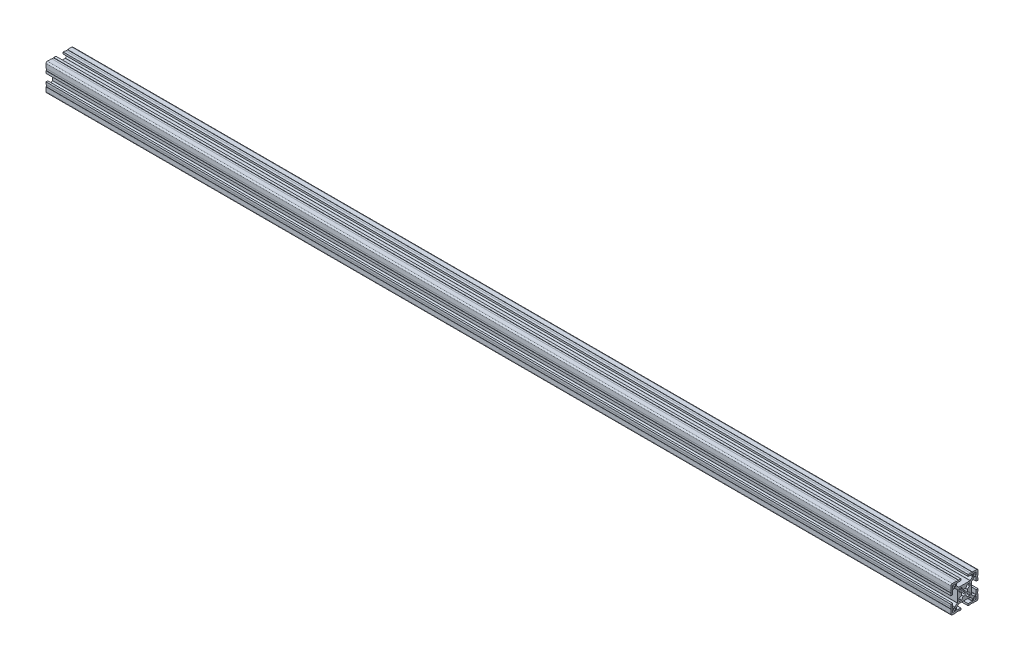
SolidWorks part; units mm, degrees
material "6063-T5"
ref_plane "Plano frontal" through (0, 0, 0) normal (0, 0, 1) x (1, 0, 0)
ref_plane "Plano superior" through (0, 0, 0) normal (0, 1, 0) x (1, 0, 0)
ref_plane "Plano direito" through (0, 0, 0) normal (1, 0, 0) x (0, 0, -1)
sketch "Esboço1" plane through (0, 0, 0) normal (0, 0, 1) x (1, 0, 0)
  line L0 (0, 0) -> (1000, 0)
  dimension "D1" = 1000
other "Quadrado PF30-11 - PERFIL 3030 CENTRO M8(1)"
ref_plane "Plano1" through (0, 0, 0) normal (1, 0, 0) x (0, 1, 0)
sketch "Sketch1" plane through (0, 0, 0) normal (1, 0, 0) x (0, 1, 0)
  line L0 (-6.1, -3.4254) -> (-6.1, -5.6)
  line L1 (-5.6, -6.1) -> (-3.4254, -6.1)
  line L2 (3.4254, -6.1) -> (5.6, -6.1)
  line L3 (6.1, -5.6) -> (6.1, -3.4254)
  line L4 (6.1, 3.4254) -> (6.1, 5.6)
  line L5 (5.6, 6.1) -> (3.4254, 6.1)
  line L6 (-3.4254, 6.1) -> (-5.6, 6.1)
  line L7 (-6.1, 5.6) -> (-6.1, 3.4254)
  line L8 (15, 6.6) -> (14.7, 6.6)
  line L9 (5.85, -2.9924) -> (3.097, -1.403)
  line L10 (10, 12.7) -> (10, 10.3)
  line L11 (13, -12.7) -> (13, -10.3)
  line L12 (-10.3, -10) -> (-12.7, -10)
  line L13 (-13, 12.7) -> (-13, 10.3)
  line L14 (3.097, 1.403) -> (5.85, 2.9924)
  line L15 (2.9924, 5.85) -> (1.403, 3.097)
  line L16 (-1.403, 3.097) -> (-2.9924, 5.85)
  line L17 (-5.85, 2.9924) -> (-3.097, 1.403)
  line L18 (-3.097, -1.403) -> (-5.85, -2.9924)
  line L19 (-2.9924, -5.85) -> (-1.403, -3.097)
  line L20 (1.403, -3.097) -> (2.9924, -5.85)
  line L21 (10.3, 10) -> (12.7, 10)
  line L22 (13, 10.3) -> (13, 12.7)
  line L23 (12.7, 13) -> (10.3, 13)
  line L24 (12.7, -10) -> (10.3, -10)
  line L25 (10, -10.3) -> (10, -12.7)
  line L26 (10.3, -13) -> (12.7, -13)
  line L27 (-13, -10.3) -> (-13, -12.7)
  line L28 (-12.7, -13) -> (-10.3, -13)
  line L29 (-10, -12.7) -> (-10, -10.3)
  line L30 (-12.7, 10) -> (-10.3, 10)
  line L31 (-10, 10.3) -> (-10, 12.7)
  line L32 (-10.3, 13) -> (-12.7, 13)
  line L33 (15, 4.05) -> (15, 6.6)
  line L34 (13, 4.05) -> (15, 4.05)
  line L35 (13, 8.7) -> (13, 4.05)
  line L36 (10.6799, 9) -> (12.7, 9)
  line L37 (7.9879, 6.4322) -> (10.4678, 8.9121)
  line L38 (7.9, -6.2201) -> (7.9, 6.2201)
  line L39 (10.4678, -8.9121) -> (7.9879, -6.4322)
  line L40 (12.7, -9) -> (10.6799, -9)
  line L41 (13, -4.05) -> (13, -8.7)
  line L42 (15, -4.05) -> (13, -4.05)
  line L43 (15, -6.6) -> (15, -4.05)
  line L44 (14.7, -6.6) -> (15, -6.6)
  line L45 (14.7, -8.8) -> (14.7, -6.6)
  line L46 (15, -8.8) -> (14.7, -8.8)
  line L47 (15, -13.5) -> (15, -8.8)
  line L48 (8.8, -15) -> (13.5, -15)
  line L49 (8.8, -14.7) -> (8.8, -15)
  line L50 (6.6, -14.7) -> (8.8, -14.7)
  line L51 (6.6, -15) -> (6.6, -14.7)
  line L52 (4.05, -15) -> (6.6, -15)
  line L53 (4.05, -13) -> (4.05, -15)
  line L54 (8.7, -13) -> (4.05, -13)
  line L55 (9, -10.6799) -> (9, -12.7)
  line L56 (6.4322, -7.9879) -> (8.9121, -10.4678)
  line L57 (-6.2201, -7.9) -> (6.2201, -7.9)
  line L58 (-8.9121, -10.4678) -> (-6.4322, -7.9879)
  line L59 (-9, -12.7) -> (-9, -10.6799)
  line L60 (-4.05, -13) -> (-8.7, -13)
  line L61 (-4.05, -15) -> (-4.05, -13)
  line L62 (-6.6, -15) -> (-4.05, -15)
  line L63 (-6.6, -14.7) -> (-6.6, -15)
  line L64 (-8.8, -14.7) -> (-6.6, -14.7)
  line L65 (-8.8, -15) -> (-8.8, -14.7)
  line L66 (-13.5, -15) -> (-8.8, -15)
  line L67 (-15, -8.8) -> (-15, -13.5)
  line L68 (-14.7, -8.8) -> (-15, -8.8)
  line L69 (-14.7, -6.6) -> (-14.7, -8.8)
  line L70 (-15, -6.6) -> (-14.7, -6.6)
  line L71 (-15, -4.05) -> (-15, -6.6)
  line L72 (-13, -4.05) -> (-15, -4.05)
  line L73 (-13, -8.7) -> (-13, -4.05)
  line L74 (-10.6799, -9) -> (-12.7, -9)
  line L75 (-7.9879, -6.4322) -> (-10.4678, -8.9121)
  line L76 (-7.9, 6.2201) -> (-7.9, -6.2201)
  line L77 (-10.4678, 8.9121) -> (-7.9879, 6.4322)
  line L78 (-12.7, 9) -> (-10.6799, 9)
  line L79 (-13, 4.05) -> (-13, 8.7)
  line L80 (-15, 4.05) -> (-13, 4.05)
  line L81 (-15, 6.6) -> (-15, 4.05)
  line L82 (-14.7, 6.6) -> (-15, 6.6)
  line L83 (-14.7, 8.8) -> (-14.7, 6.6)
  line L84 (-15, 8.8) -> (-14.7, 8.8)
  line L85 (-15, 13.5) -> (-15, 8.8)
  line L86 (-8.8, 15) -> (-13.5, 15)
  line L87 (-8.8, 14.7) -> (-8.8, 15)
  line L88 (-6.6, 14.7) -> (-8.8, 14.7)
  line L89 (-6.6, 15) -> (-6.6, 14.7)
  line L90 (-4.05, 15) -> (-6.6, 15)
  line L91 (-4.05, 13) -> (-4.05, 15)
  line L92 (-8.7, 13) -> (-4.05, 13)
  line L93 (-9, 10.6799) -> (-9, 12.7)
  line L94 (-6.4322, 7.9879) -> (-8.9121, 10.4678)
  line L95 (6.2201, 7.9) -> (-6.2201, 7.9)
  line L96 (8.9121, 10.4678) -> (6.4322, 7.9879)
  line L97 (9, 12.7) -> (9, 10.6799)
  line L98 (4.05, 13) -> (8.7, 13)
  line L99 (4.05, 15) -> (4.05, 13)
  line L100 (6.6, 15) -> (4.05, 15)
  line L101 (6.6, 14.7) -> (6.6, 15)
  line L102 (8.8, 14.7) -> (6.6, 14.7)
  line L103 (8.8, 15) -> (8.8, 14.7)
  line L104 (13.5, 15) -> (8.8, 15)
  line L105 (15, 8.8) -> (15, 13.5)
  line L106 (14.7, 8.8) -> (15, 8.8)
  line L107 (14.7, 6.6) -> (14.7, 8.8)
  arc A0 (-5.85, -2.9924) -> (-6.1, -3.4254) centre (-5.6, -3.4254) ccw
  arc A1 (-6.1, -5.6) -> (-5.6, -6.1) centre (-5.6, -5.6) ccw
  arc A2 (-3.4254, -6.1) -> (-2.9924, -5.85) centre (-3.4254, -5.6) ccw
  arc A3 (2.9924, -5.85) -> (3.4254, -6.1) centre (3.4254, -5.6) ccw
  arc A4 (5.6, -6.1) -> (6.1, -5.6) centre (5.6, -5.6) ccw
  arc A5 (6.1, -3.4254) -> (5.85, -2.9924) centre (5.6, -3.4254) ccw
  arc A6 (5.85, 2.9924) -> (6.1, 3.4254) centre (5.6, 3.4254) ccw
  arc A7 (6.1, 5.6) -> (5.6, 6.1) centre (5.6, 5.6) ccw
  arc A8 (3.4254, 6.1) -> (2.9924, 5.85) centre (3.4254, 5.6) ccw
  arc A9 (-2.9924, 5.85) -> (-3.4254, 6.1) centre (-3.4254, 5.6) ccw
  arc A10 (-5.6, 6.1) -> (-6.1, 5.6) centre (-5.6, 5.6) ccw
  arc A11 (-6.1, 3.4254) -> (-5.85, 2.9924) centre (-5.6, 3.4254) ccw
  arc A12 (3.097, -1.403) -> (3.097, 1.403) centre (0, 0) ccw
  arc A13 (1.403, 3.097) -> (-1.403, 3.097) centre (0, 0) ccw
  arc A14 (-3.097, 1.403) -> (-3.097, -1.403) centre (0, 0) ccw
  arc A15 (-1.403, -3.097) -> (1.403, -3.097) centre (0, 0) ccw
  arc A16 (10, 10.3) -> (10.3, 10) centre (10.3, 10.3) ccw
  arc A17 (12.7, 10) -> (13, 10.3) centre (12.7, 10.3) ccw
  arc A18 (13, 12.7) -> (12.7, 13) centre (12.7, 12.7) ccw
  arc A19 (10.3, 13) -> (10, 12.7) centre (10.3, 12.7) ccw
  arc A20 (13, -10.3) -> (12.7, -10) centre (12.7, -10.3) ccw
  arc A21 (10.3, -10) -> (10, -10.3) centre (10.3, -10.3) ccw
  arc A22 (10, -12.7) -> (10.3, -13) centre (10.3, -12.7) ccw
  arc A23 (12.7, -13) -> (13, -12.7) centre (12.7, -12.7) ccw
  arc A24 (-12.7, -10) -> (-13, -10.3) centre (-12.7, -10.3) ccw
  arc A25 (-13, -12.7) -> (-12.7, -13) centre (-12.7, -12.7) ccw
  arc A26 (-10.3, -13) -> (-10, -12.7) centre (-10.3, -12.7) ccw
  arc A27 (-10, -10.3) -> (-10.3, -10) centre (-10.3, -10.3) ccw
  arc A28 (-13, 10.3) -> (-12.7, 10) centre (-12.7, 10.3) ccw
  arc A29 (-10.3, 10) -> (-10, 10.3) centre (-10.3, 10.3) ccw
  arc A30 (-10, 12.7) -> (-10.3, 13) centre (-10.3, 12.7) ccw
  arc A31 (-12.7, 13) -> (-13, 12.7) centre (-12.7, 12.7) ccw
  arc A32 (13, 8.7) -> (12.7, 9) centre (12.7, 8.7) ccw
  arc A33 (10.6799, 9) -> (10.4678, 8.9121) centre (10.6799, 8.7) ccw
  arc A34 (7.9879, 6.4322) -> (7.9, 6.2201) centre (8.2, 6.2201) ccw
  arc A35 (7.9, -6.2201) -> (7.9879, -6.4322) centre (8.2, -6.2201) ccw
  arc A36 (10.4678, -8.9121) -> (10.6799, -9) centre (10.6799, -8.7) ccw
  arc A37 (12.7, -9) -> (13, -8.7) centre (12.7, -8.7) ccw
  arc A38 (13.5, -15) -> (15, -13.5) centre (13.5, -13.5) ccw
  arc A39 (8.7, -13) -> (9, -12.7) centre (8.7, -12.7) ccw
  arc A40 (9, -10.6799) -> (8.9121, -10.4678) centre (8.7, -10.6799) ccw
  arc A41 (6.4322, -7.9879) -> (6.2201, -7.9) centre (6.2201, -8.2) ccw
  arc A42 (-6.2201, -7.9) -> (-6.4322, -7.9879) centre (-6.2201, -8.2) ccw
  arc A43 (-8.9121, -10.4678) -> (-9, -10.6799) centre (-8.7, -10.6799) ccw
  arc A44 (-9, -12.7) -> (-8.7, -13) centre (-8.7, -12.7) ccw
  arc A45 (-15, -13.5) -> (-13.5, -15) centre (-13.5, -13.5) ccw
  arc A46 (-13, -8.7) -> (-12.7, -9) centre (-12.7, -8.7) ccw
  arc A47 (-10.6799, -9) -> (-10.4678, -8.9121) centre (-10.6799, -8.7) ccw
  arc A48 (-7.9879, -6.4322) -> (-7.9, -6.2201) centre (-8.2, -6.2201) ccw
  arc A49 (-7.9, 6.2201) -> (-7.9879, 6.4322) centre (-8.2, 6.2201) ccw
  arc A50 (-10.4678, 8.9121) -> (-10.6799, 9) centre (-10.6799, 8.7) ccw
  arc A51 (-12.7, 9) -> (-13, 8.7) centre (-12.7, 8.7) ccw
  arc A52 (-13.5, 15) -> (-15, 13.5) centre (-13.5, 13.5) ccw
  arc A53 (-8.7, 13) -> (-9, 12.7) centre (-8.7, 12.7) ccw
  arc A54 (-9, 10.6799) -> (-8.9121, 10.4678) centre (-8.7, 10.6799) ccw
  arc A55 (-6.4322, 7.9879) -> (-6.2201, 7.9) centre (-6.2201, 8.2) ccw
  arc A56 (6.2201, 7.9) -> (6.4322, 7.9879) centre (6.2201, 8.2) ccw
  arc A57 (8.9121, 10.4678) -> (9, 10.6799) centre (8.7, 10.6799) ccw
  arc A58 (9, 12.7) -> (8.7, 13) centre (8.7, 12.7) ccw
  arc A59 (15, 13.5) -> (13.5, 15) centre (13.5, 13.5) ccw
  point P1 (0, 0)
  point P2 (0, 0)
  point P3 (-15, -15)
  point P4 (0, -15)
  point P5 (-15, 0)
  point P230 (-15, 15)
  point P231 (0, 15)
  point P232 (15, 15)
  point P233 (15, 0)
  point P234 (15, -15)
  point P235 (0, -15)
  point P236 (-15, -15)
  point P237 (-15, 0)
  point P238 (0, 0)
  point P239 (0, 0)
